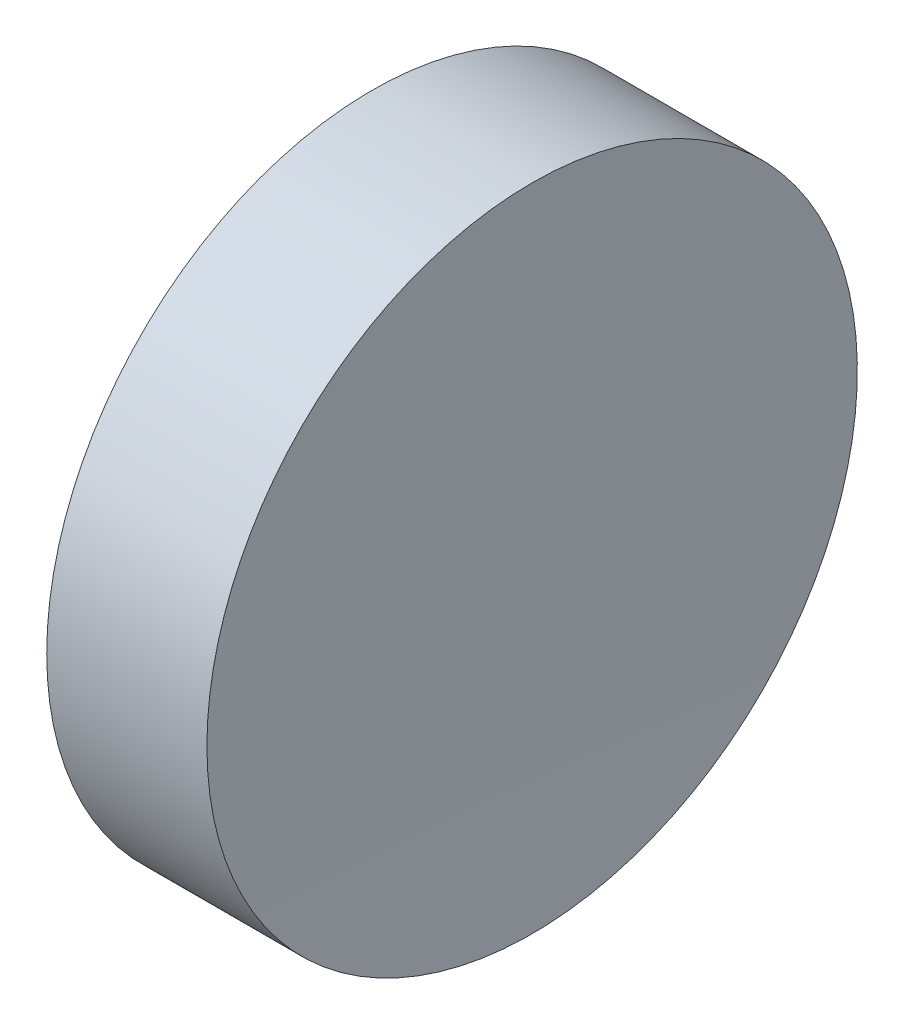
SolidWorks part; units mm, degrees
ref_plane "前视基准面" through (0, 0, 0) normal (0, 0, 1) x (1, 0, 0)
ref_plane "上视基准面" through (0, 0, 0) normal (0, 1, 0) x (1, 0, 0)
ref_plane "右视基准面" through (0, 0, 0) normal (1, 0, 0) x (0, 0, -1)
sketch "草图1" plane through (0, 0, 0) normal (0, 0, 1) x (1, 0, 0)
  line L0 (108.9851, 69.378) -> (132.7763, 69.378) construction
  line L1 (115.0927, 69.378) -> (115.0927, 81.878)
  line L2 (115.0927, 81.878) -> (121.2489, 81.878)
  line L3 (121.0927, 69.378) -> (115.0927, 69.378)
  arc A0 (121.2489, 81.878) -> (121.0927, 69.378) centre (621.0927, 69.378) ccw
  point P8 (121.6242, 69.378)
  dimension "D1" = 6.1563
  dimension "D2" = 12.5
revolve "旋转1" add sketch "草图1" angle 360 about L0
